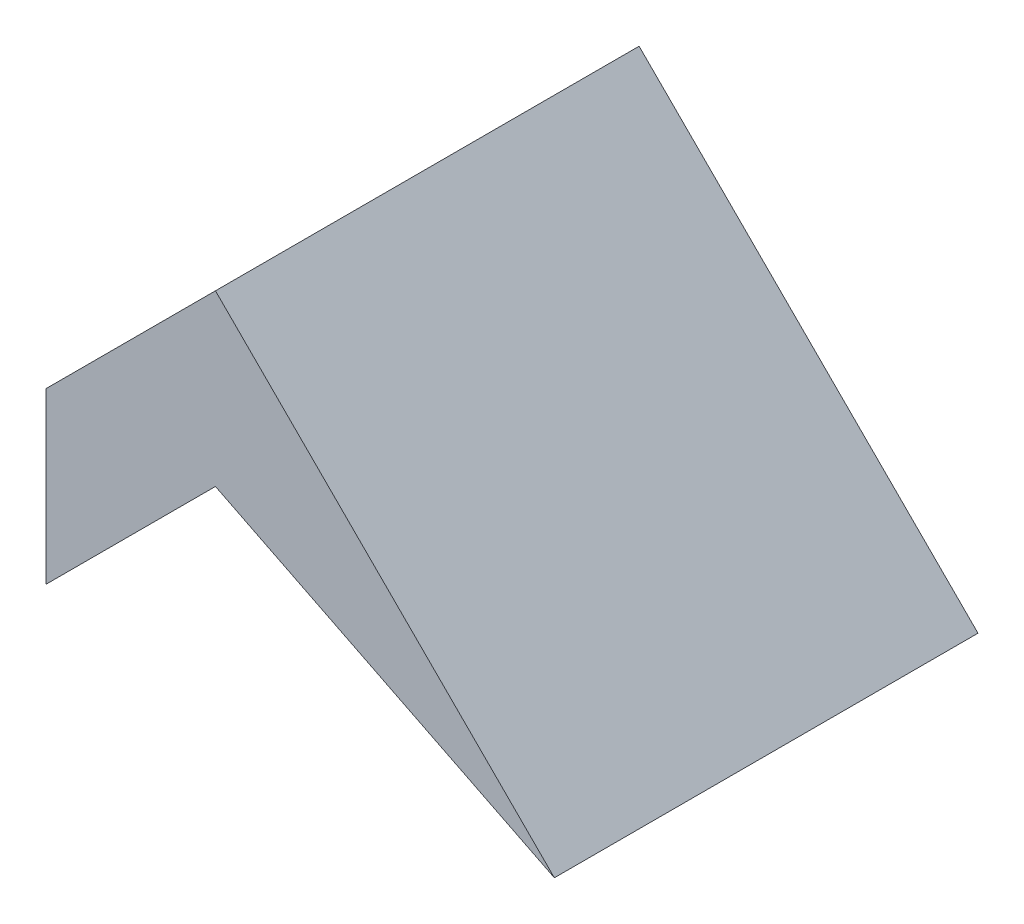
SolidWorks part; units mm, degrees
ref_plane "Front Plane" through (0, 0, 0) normal (0, 0, 1) x (1, 0, 0)
ref_plane "Top Plane" through (0, 0, 0) normal (0, 1, 0) x (1, 0, 0)
ref_plane "Right Plane" through (0, 0, 0) normal (1, 0, 0) x (0, 0, -1)
sketch "Sketch1" plane through (0, 0, 0) normal (0, 0, 1) x (1, 0, 0)
  line L0 (-10, -10) -> (0, 0)
  line L1 (0, 0) -> (20, -20)
  line L2 (20, -20) -> (0, -10)
  line L3 (0, -10) -> (-10, -20)
  line L4 (-10, -20) -> (-10, -10)
  dimension "D1" = 10
  dimension "D2" = 10
  dimension "D3" = 10
extrude "Boss-Extrude3" add sketch "Sketch1" along normal blind 25
